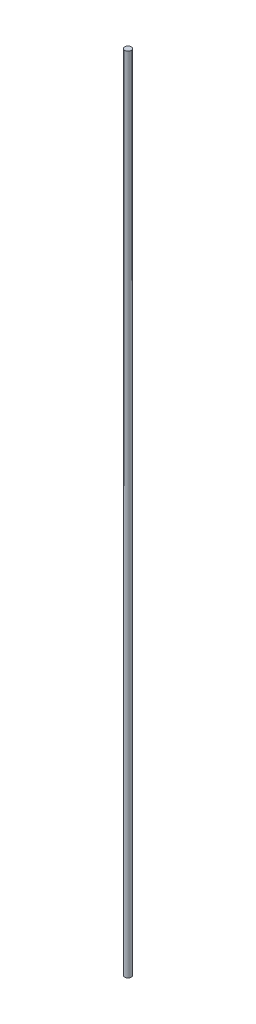
SolidWorks part; units mm, degrees
material "AISI 304"
ref_plane "Front Plane" through (0, 0, 0) normal (0, 0, 1) x (1, 0, 0)
ref_plane "Top Plane" through (0, 0, 0) normal (0, 1, 0) x (1, 0, 0)
ref_plane "Right Plane" through (0, 0, 0) normal (1, 0, 0) x (0, 0, -1)
sketch "Sketch1" plane through (0, 0, 0) normal (0, 1, 0) x (1, 0, 0)
  circle A0 centre (0, 0) radius 4
  dimension "D1" = 8
extrude "Boss-Extrude1" add sketch "Sketch1" along normal blind 1000
